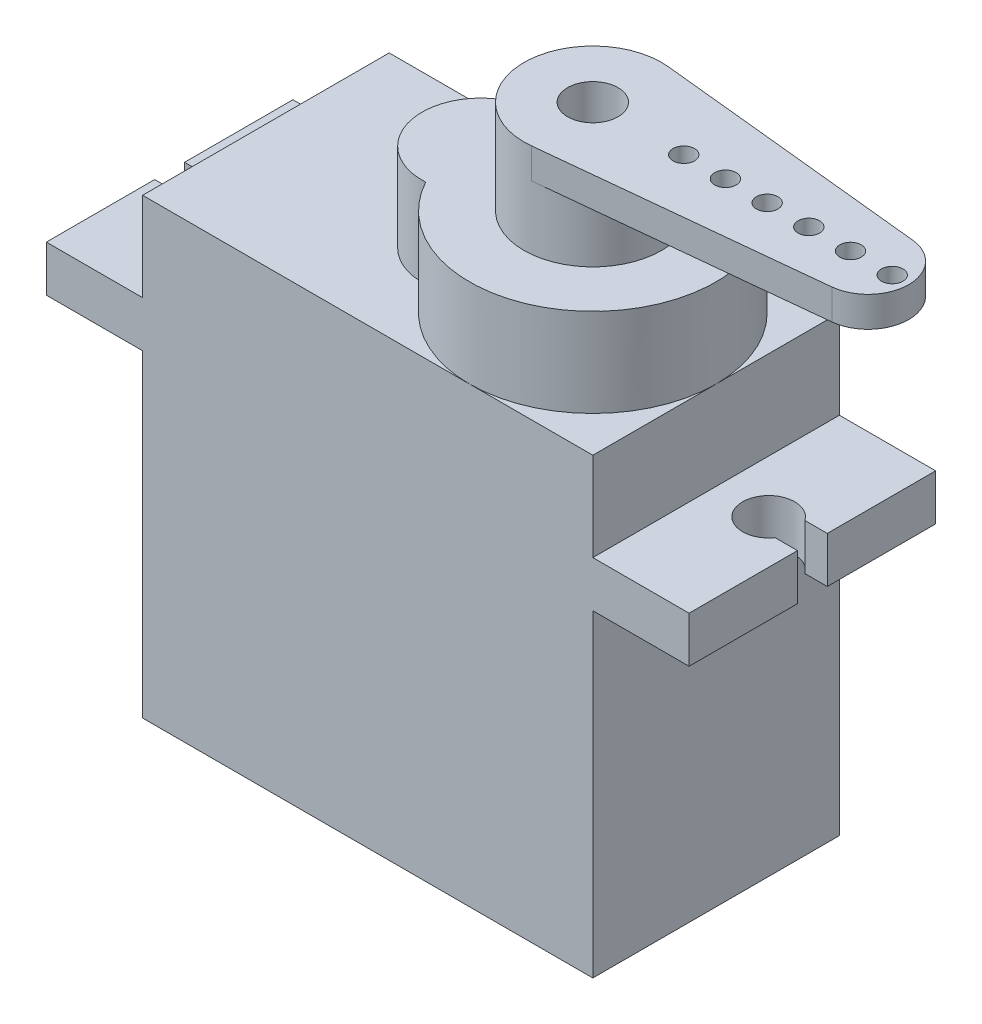
SolidWorks part; units mm, degrees
ref_plane "Front Plane" through (0, 0, 0) normal (0, 0, 1) x (1, 0, 0)
ref_plane "Top Plane" through (0, 0, 0) normal (0, 1, 0) x (1, 0, 0)
ref_plane "Right Plane" through (0, 0, 0) normal (1, 0, 0) x (0, 0, -1)
sketch "Sketch1" plane through (0, 0, 0) normal (0, 1, 0) x (1, 0, 0)
  line L1 (-11.3157, -6.1976) -> (11.3157, -6.1976)
  line L2 (-11.3157, -6.1976) -> (-11.3157, 6.1976)
  line L3 (-11.3157, 6.1976) -> (11.3157, 6.1976)
  line L4 (11.3157, -6.1976) -> (11.3157, 6.1976)
  line L5 (-11.3157, -6.1976) -> (11.3157, 6.1976) construction
  line L6 (-11.3157, 6.1976) -> (11.3157, -6.1976) construction
  point P0 (0, 0)
  dimension "D1" = 12.3952
  dimension "D2" = 22.6314
extrude "Boss-Extrude1" add sketch "Sketch1" along normal blind 22.7584
sketch "Sketch2" plane through (0, 22.7584, 0) normal (0, 1, 0) x (1, 0, 0)
  line L0 (11.3157, -6.1976) -> (11.3157, 6.1976) construction
  line L1 (11.3157, 6.1976) -> (-11.3157, 6.1976) construction
  line L2 (-11.3157, -6.1976) -> (11.3157, -6.1976) construction
  line L3 (-0.508, 2.9591) -> (-0.3274, 2.9591)
  line L4 (-0.508, -2.9591) -> (-0.3274, -2.9591)
  line L5 (-3.4671, 0) -> (11.3157, 0) construction
  arc A0 (-0.3303, -2.9538) -> (-0.3303, 2.9538) centre (5.1181, 0) ccw
  arc A1 (-0.3303, 2.9538) -> (-0.3303, -2.9538) centre (-0.508, 0) ccw
  dimension "D1" = 5.9182
  dimension "D2" = 14.7828
extrude "Boss-Extrude2" add sketch "Sketch2" along normal blind 4.445 contours A1 L5 A0 | L5 A1 A0
sketch "Sketch3" plane through (0, 27.2034, 0) normal (0, 1, 0) x (1, 0, 0)
  circle A0 centre (5.1181, 0) radius 3.4608
  arc A1 (-0.3303, -2.9538) -> (-0.3303, 2.9538) centre (5.1181, 0) ccw construction
  dimension "D1" = 6.9215
extrude "Boss-Extrude3" add sketch "Sketch3" along normal blind 4.7244
sketch "Sketch4" plane through (0, 31.9278, 0) normal (0, 1, 0) x (1, 0, 0)
  line L0 (5.4723, 3.4426) -> (19.164, 2.034)
  line L1 (5.4723, -3.4426) -> (19.164, -2.034)
  line L2 (1.6574, 0) -> (20.9994, 0) construction
  line L3 (1.6574, 0) -> (9.1504, 0) construction
  arc A0 (19.164, -2.034) -> (19.164, 2.034) centre (18.9548, 0) ccw
  circle A1 centre (5.1181, 0) radius 3.4608 construction
  circle A2 centre (11.7856, 0) radius 0.5397
  circle A3 centre (5.1181, 0) radius 3.4608 construction
  circle A4 centre (9.6901, 0) radius 0.5398
  circle A5 centre (5.1181, 0) radius 3.4608
  arc A6 (5.4723, 3.4426) -> (5.4723, -3.4426) centre (5.1181, 0) ccw
  circle A7 centre (13.8811, 0) radius 0.5398
  circle A8 centre (15.9766, 0) radius 0.5398
  circle A9 centre (18.0721, 0) radius 0.5397
  circle A10 centre (20.1676, 0) radius 0.5397
  dimension "D1" = 4.0894
  dimension "D4" = 1.0795
  dimension "D3" = 19.3421
  dimension "D5" = 7.493
  dimension "D7" = 2.0955
  dimension "D2" = 0
  dimension "D6" = 6
extrude "Boss-Extrude4" add sketch "Sketch4" against normal blind 1.524
ref_plane "Plane1" through (0, 18.3007, 0) normal (0, 1, 0) x (1, 0, 0)
sketch "Sketch5" plane through (0, 18.3007, 0) normal (0, 1, 0) x (1, 0, 0)
  line L0 (11.3157, 6.1976) -> (5.1181, 6.1976) construction
  line L1 (-16.1544, -6.1976) -> (16.1544, -6.1976)
  line L2 (-16.1544, -6.1976) -> (-16.1544, -0.7493)
  line L3 (-16.1544, 6.1976) -> (16.1544, 6.1976)
  line L4 (16.1544, -6.1976) -> (16.1544, -0.7493)
  line L5 (-16.1544, -6.1976) -> (16.1544, 6.1976) construction
  line L6 (-16.1544, 6.1976) -> (16.1544, -6.1976) construction
  line L7 (-16.1544, -0.7493) -> (-15.0295, -0.7493)
  line L8 (-16.1544, 0.7493) -> (-15.0295, 0.7493)
  line L9 (-12.6492, 0) -> (-16.1544, 0) construction
  line L10 (-16.1544, 0.7493) -> (-16.1544, 6.1976)
  line L11 (0, -6.8174) -> (0, 6.8174) construction
  line L12 (16.1544, -0.7493) -> (15.0295, -0.7493)
  line L13 (16.1544, 0.7493) -> (15.0295, 0.7493)
  line L14 (16.1544, 0.7493) -> (16.1544, 6.1976)
  arc A0 (-15.0295, -0.7493) -> (-15.0295, 0.7493) centre (-13.9573, 0) ccw
  arc A1 (15.0295, -0.7493) -> (15.0295, 0.7493) centre (13.9573, 0) cw
  point P0 (0, 0)
  point P9 (0, 0)
  dimension "D2" = 1.3081
  dimension "D1" = 32.3088
  dimension "D3" = 5.4483
  dimension "D4" = 5.4483
  dimension "D5" = 3.5052
extrude "Boss-Extrude5" add sketch "Sketch5" against normal blind 2.3114
sketch "Sketch6" plane through (0, 31.9278, 0) normal (0, 1, 0) x (1, 0, 0)
  circle A0 centre (5.1181, 0) radius 1.27
  arc A1 (5.4723, 3.4426) -> (5.4723, -3.4426) centre (5.1181, 0) ccw construction
  dimension "D1" = 2.54
extrude "Cut-Extrude1" cut sketch "Sketch6" against normal up to surface (4.7244 mm away) up to face at (5.1181, 27.2034, 3.4608)
